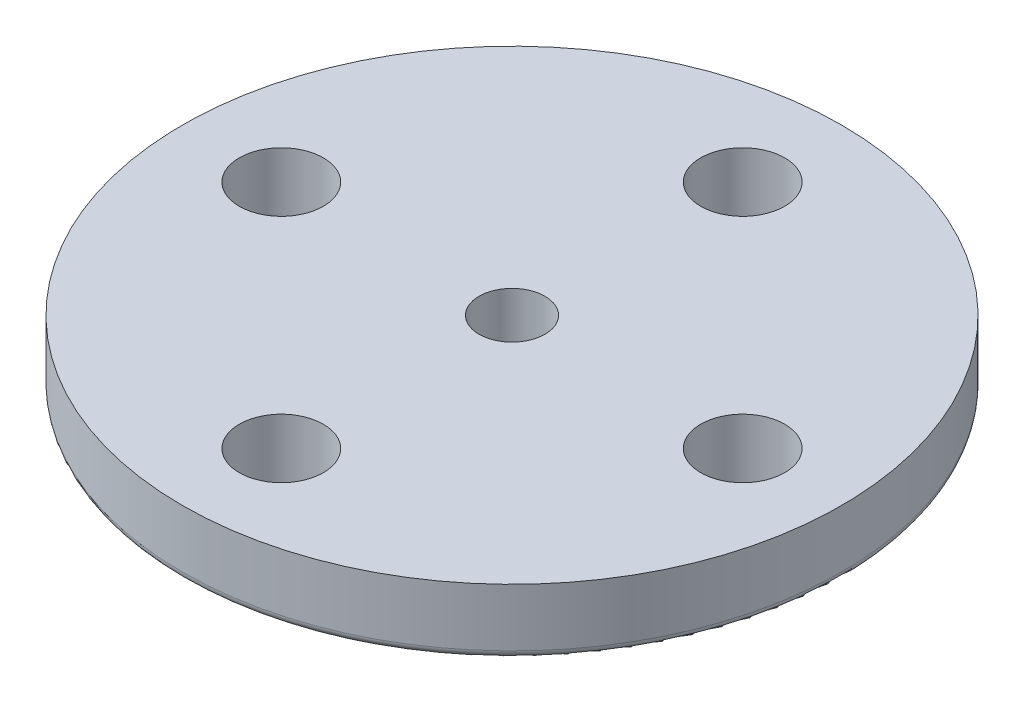
SolidWorks part; units mm, degrees
material "ABS"
ref_plane "Front Plane" through (0, 0, 0) normal (0, 0, 1) x (1, 0, 0)
ref_plane "Top Plane" through (0, 0, 0) normal (0, 1, 0) x (1, 0, 0)
ref_plane "Right Plane" through (0, 0, 0) normal (1, 0, 0) x (0, 0, -1)
sketch "Sketch1" plane through (0, 0, 0) normal (0, 1, 0) x (1, 0, 0)
  circle A0 centre (0, 0) radius 10
  dimension "D1" = 20
extrude "Boss-Extrude1" add sketch "Sketch1" along normal blind 2
sketch "Sketch2" plane through (0, 0, 0) normal (0, 1, 0) x (1, 0, 0)
  circle A0 centre (0, 0) radius 4.5
  dimension "D1" = 9
extrude "Boss-Extrude2" add sketch "Sketch2" against normal blind 2.5
sketch "Sketch3" plane through (0, 0, 0) normal (0, 1, 0) x (1, 0, 0)
  line L0 (0, 16.6668) -> (0, -17.2828) construction
  line L1 (-21.9372, 0) -> (30.2192, 0) construction
  line L2 (-7, 16.6668) -> (-7, -16.6668) construction
  line L3 (-15.9139, 7) -> (17.4197, 7) construction
  circle A0 centre (0, 7) radius 1.275
  circle A1 centre (-7, 0) radius 1.275
  circle A2 centre (0, -7) radius 1.275
  circle A3 centre (7, 0) radius 1.275
  dimension "D3" = 2.55
  dimension "D4" = 2.55
  dimension "D1" = 7
  dimension "D2" = 7
extrude "Cut-Extrude1" cut sketch "Sketch3" along normal through all
cosmetic thread "Cosmetic Thread1" parameters "D2"=2.87
cosmetic thread "Cosmetic Thread2" parameters "D2"=2.87
cosmetic thread "Cosmetic Thread3" parameters "D2"=2.87
cosmetic thread "Cosmetic Thread4" parameters "D2"=2.87
fillet "Fillet1" radius 0.25 1 edges at (0, 0, 10)
sketch "Sketch6" plane through (0, 2, 0) normal (0, 1, 0) x (1, 0, 0)
  circle A0 centre (0, 0) radius 1
  dimension "D1" = 2
extrude "Cut-Extrude2" cut sketch "Sketch6" against normal through all
sketch "Sketch7" plane through (0, -2.5, 0) normal (0, -1, 0) x (1, 0, 0)
  circle A0 centre (0, 0) radius 2.9
  dimension "D1" = 5.8
extrude "Cut-Extrude3" cut sketch "Sketch7" against normal blind 2.5
sketch3d "3DSketch1"
  line L0 (0, 0, 0) -> (0, -47.4119, 0) construction
sketch "Sketch8" plane through (0, -2.5, 0) normal (0, -1, 0) x (1, 0, 0)
  line L1 (-2.3524, -1.0465) -> (-2.7456, -0.9337)
  line L2 (-2.3524, -1.0465) -> (-2.5319, -1.4141)
  arc A1 (-2.7456, -0.9337) -> (-2.5319, -1.4141) centre (0, 0) ccw
  circle A4 centre (0, 0) radius 2.9 construction
  dimension "D4" = 0.409
  dimension "D3" = 5.8
  dimension "D1" = 80
  dimension "D2" = 0.5258
extrude "Boss-Extrude4" add sketch "Sketch8" against normal blind 2.5
pattern_circular "CirPattern1" count 26 over 360 about axis through (0, 0, 0) along (0, 1, 0) of "Boss-Extrude4"
